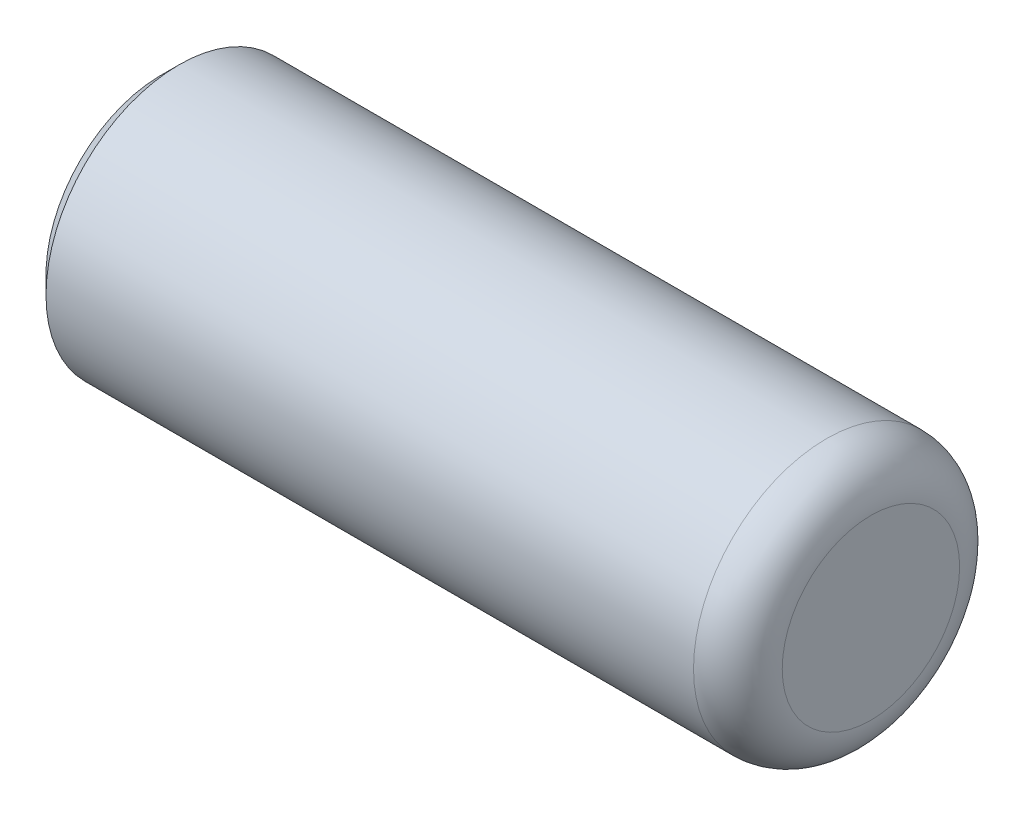
SolidWorks part; units mm, degrees
material "SUJ"
ref_plane "Front Plane" through (0, 0, 0) normal (0, 0, 1) x (1, 0, 0)
ref_plane "Top Plane" through (0, 0, 0) normal (0, 1, 0) x (1, 0, 0)
ref_plane "Right Plane" through (0, 0, 0) normal (1, 0, 0) x (0, 0, -1)
sketch "Sketch1" plane through (0, 0, 0) normal (1, 0, 0) x (0, -1, 0)
  circle A0 centre (0, 0) radius 1.5
  dimension "D1" = 3
extrude "Boss-Extrude1" add sketch "Sketch1" along normal mid plane 8
fillet "Fillet1" radius 0.5 1 edges at (4, 0, -1.5)
chamfer "Chamfer1" distance 0.2 angle 45 1 edges at (-4, 0, -1.5)
